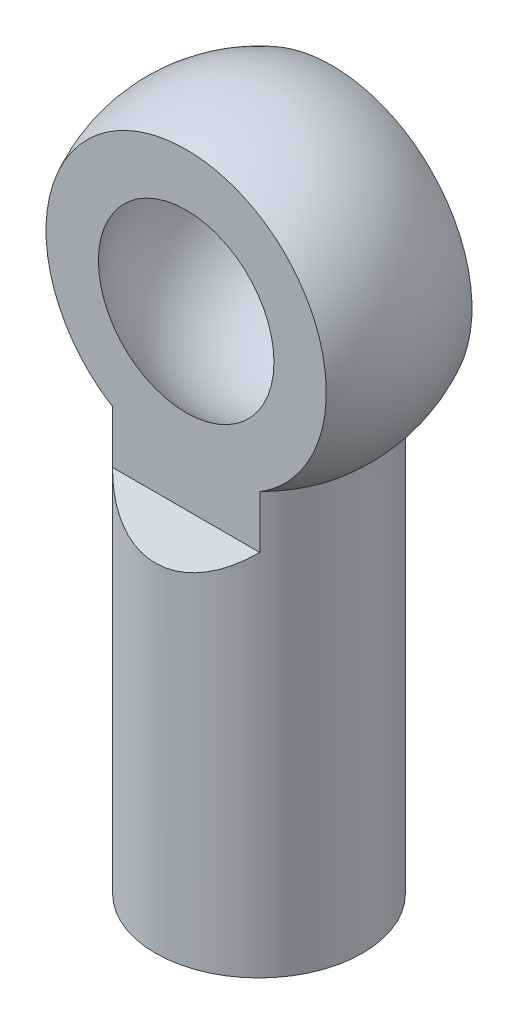
SolidWorks part; units mm, degrees
ref_plane "Front Plane" through (0, 0, 0) normal (0, 0, 1) x (1, 0, 0)
ref_plane "Top Plane" through (0, 0, 0) normal (0, 1, 0) x (1, 0, 0)
ref_plane "Right Plane" through (0, 0, 0) normal (1, 0, 0) x (0, 0, -1)
sketch "Sketch1" plane through (0, 0, 0) normal (0, 1, 0) x (1, 0, 0)
  circle A0 centre (0, 0) radius 2.95
  dimension "D1" = 5.9
extrude "Boss-Extrude1" add sketch "Sketch1" along normal blind 12
sketch "Sketch2" plane through (0, 0, 0) normal (1, 0, 0) x (0, 0, -1)
  line L0 (0, 19.8982) -> (0, 10.8982)
  arc A0 (0, 10.8982) -> (0, 19.8982) centre (0, 15.3982) ccw
  dimension "D1" = 9
sketch "Sketch5" plane through (0, 0, 0) normal (0, -1, 0) x (1, 0, 0)
  circle A0 centre (0, 0) radius 1.5
  dimension "D1" = 3
extrude "Cut-Extrude3" cut sketch "Sketch5" against normal blind 11
ref_axis "Axis2" through (0, 12, 0) along (0, -1, 0)
revolve "Revolve3" add sketch "Sketch2" angle 360 about axis through (0, 12, 0) along (0, -1, 0)
sketch "Sketch8" plane through (0, 0, 0) normal (1, 0, 0) x (0, 0, -1)
  line L0 (-2.075, 20.3908) -> (-2.075, 10.5)
  line L1 (-2.075, 10.5) -> (-5.08, 7.495)
  line L2 (-5.08, 7.495) -> (-5.08, 20.3908)
  line L3 (-5.08, 20.3908) -> (-2.075, 20.3908)
  line L4 (0, 12) -> (0, 0) construction
  line L5 (0, 0) -> (0, 19.8982) construction
  line L6 (5.08, 20.3908) -> (2.075, 20.3908)
  line L7 (5.08, 7.495) -> (5.08, 20.3908)
  line L8 (2.075, 10.5) -> (5.08, 7.495)
  line L9 (2.075, 20.3908) -> (2.075, 10.5)
  line L10 (-2.95, 0) -> (2.95, 0) construction
  arc A0 (2.95, 12) -> (-2.95, 12) centre (0, 15.3982) ccw construction
  dimension "D1" = 5.08
  dimension "D2" = 4.15
  dimension "D3" = 10.5
  dimension "D4" = 45
extrude "Cut-Extrude4" cut sketch "Sketch8" against normal through all both and the other way through all
sketch "Sketch9" plane through (0, 0, 2.075) normal (0, 0, 1) x (1, 0, 0)
  point P0 (0, 15.3982)
sketch "Sketch10" plane through (0, 0, -2.075) normal (0, 0, -1) x (-1, 0, 0)
  point P0 (0, 15.3982)
ref_axis "Axis3" through (0, 15.3982, 2.075) along (0, 0, -1)
ref_plane "Plane2" through (0, 0, 0) normal (1, 0, 0) x (0, 0, -1)
sketch "Sketch11" plane through (0, 0, 0) normal (1, 0, 0) x (0, 0, -1)
  line L0 (-2.075, 15.3982) -> (2.075, 15.3982) construction
  line L1 (-3.25, 15.3982) -> (3.25, 15.3982)
  arc A0 (3.25, 15.3982) -> (-3.25, 15.3982) centre (0, 15.3982) ccw
  dimension "D1" = 6.5
revolve "Cut-Revolve2" cut sketch "Sketch11" angle 360 about axis through (0, 15.3982, 2.075) along (0, 0, -1)
sketch "Sketch12" plane through (0, 0, -2.075) normal (0, 0, -1) x (-1, 0, 0)
  circle A0 centre (0, 15.3982) radius 2.5014 construction
  circle A1 centre (0, 15.3982) radius 2.5014
  circle A2 centre (0, 15.3982) radius 3.4
  dimension "D1" = 6.8
extrude "Boss-Extrude5" add sketch "Sketch12" along normal blind 0.02
ref_plane "Plane3" through (0, 15.3982, 0) normal (0, -1, 0) x (0, 0, -1)
